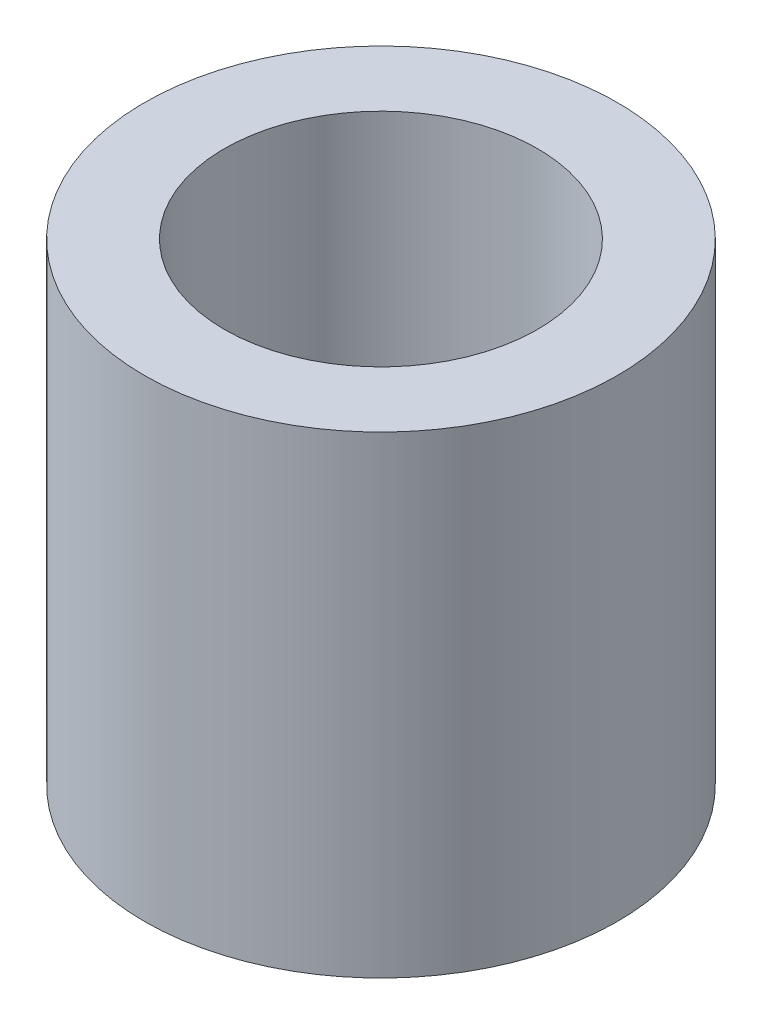
SolidWorks part; units mm, degrees
ref_plane "Front Plane" through (0, 0, 0) normal (0, 0, 1) x (1, 0, 0)
ref_plane "Top Plane" through (0, 0, 0) normal (0, 1, 0) x (1, 0, 0)
ref_plane "Right Plane" through (0, 0, 0) normal (1, 0, 0) x (0, 0, -1)
sketch "Sketch1" plane through (0, 0, 0) normal (0, 1, 0) x (1, 0, 0)
  circle A0 centre (0, 0) radius 10
  circle A1 centre (0, 0) radius 4.5
  dimension "D1" = 20
  dimension "D2" = 9
extrude "Boss-Extrude1" add sketch "Sketch1" along normal blind 20
sketch "Sketch2" plane through (0, 20, 0) normal (0, 1, 0) x (1, 0, 0)
  circle A0 centre (0, 0) radius 6.625
  dimension "D1" = 13.25
extrude "Cut-Extrude1" cut sketch "Sketch2" against normal blind 13
sketch "Sketch3" plane through (0, 0, 0) normal (0, -1, 0) x (1, 0, 0)
  circle A0 centre (0, 0) radius 6.625
  dimension "D1" = 13.25
extrude "Cut-Extrude2" cut sketch "Sketch3" against normal blind 5
